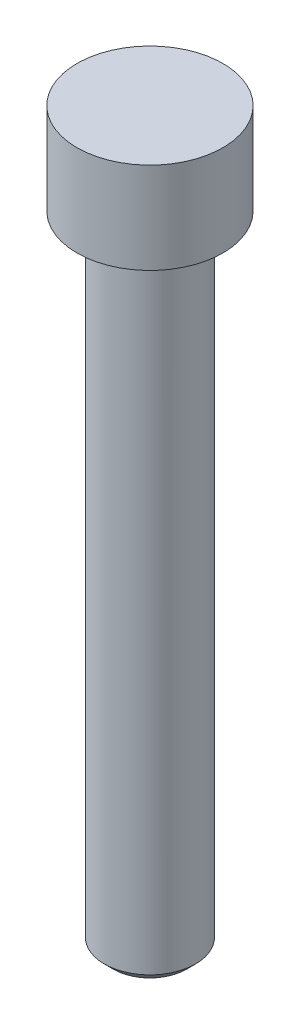
SolidWorks part; units mm, degrees
ref_plane "Front Plane" through (0, 0, 0) normal (0, 0, 1) x (1, 0, 0)
ref_plane "Top Plane" through (0, 0, 0) normal (0, 1, 0) x (1, 0, 0)
ref_plane "Right Plane" through (0, 0, 0) normal (1, 0, 0) x (0, 0, -1)
sketch "Sketch1" plane through (0, 0, 0) normal (0, 1, 0) x (1, 0, 0)
  circle A0 centre (0, 0) radius 8
  dimension "D1" = 16
extrude "Boss-Extrude1" add sketch "Sketch1" along normal blind 10
sketch "Sketch2" plane through (0, 0, 0) normal (0, -1, 0) x (1, 0, 0)
  circle A0 centre (0, 0) radius 5
  dimension "D1" = 10
extrude "Boss-Extrude2" add sketch "Sketch2" along normal blind 70
chamfer "Chamfer1" distance 1 angle 45 1 edges at (0, -70, -5)
